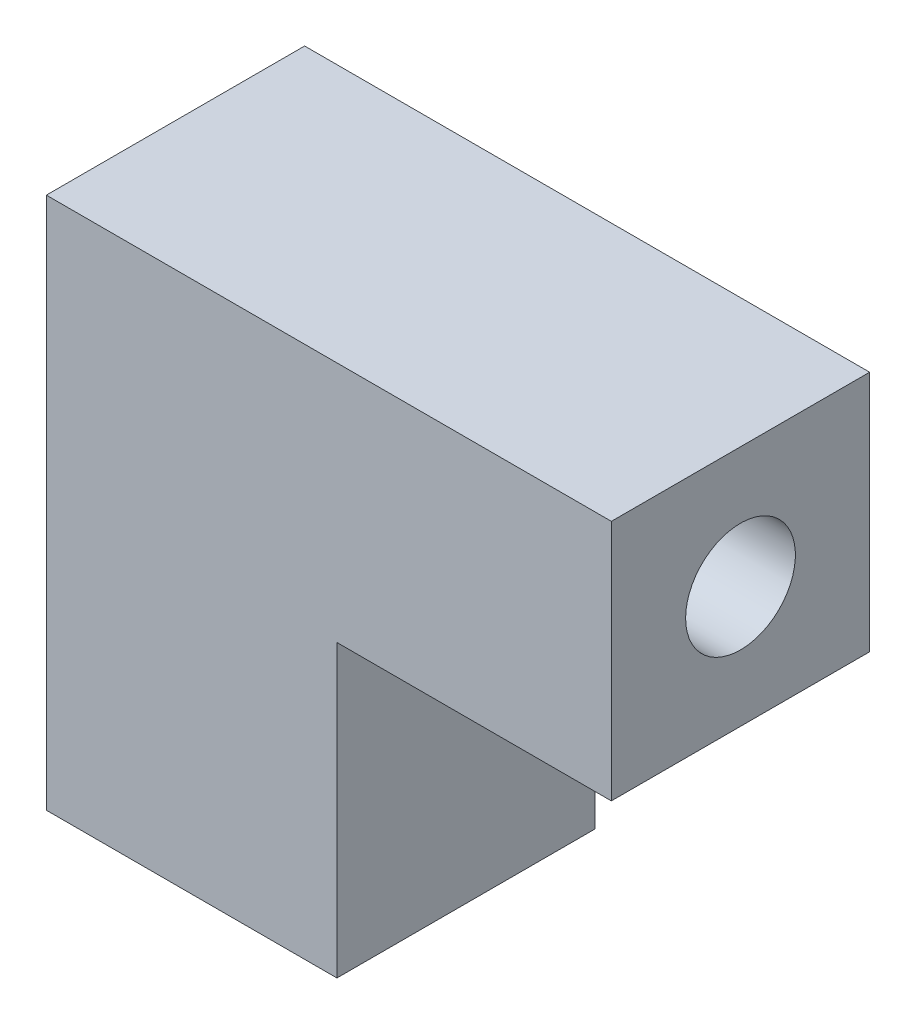
SolidWorks part; units mm, degrees
ref_plane "정면" through (0, 0, 0) normal (0, 0, 1) x (1, 0, 0)
ref_plane "윗면" through (0, 0, 0) normal (0, 1, 0) x (1, 0, 0)
ref_plane "우측면" through (0, 0, 0) normal (1, 0, 0) x (0, 0, -1)
sketch "스케치1" plane through (0, 0, 0) normal (0, 0, 1) x (1, 0, 0)
  line L0 (0, 0) -> (0, 33)
  line L1 (0, 33) -> (35, 33)
  line L2 (35, 33) -> (35, 18)
  line L3 (35, 18) -> (18, 18)
  line L4 (18, 18) -> (18, 0)
  line L5 (18, 0) -> (0, 0)
  dimension "D1" = 35
  dimension "D2" = 15
  dimension "D3" = 33
  dimension "D4" = 17
extrude "보스-돌출1" add sketch "스케치1" along normal mid plane 16
hole_wizard "M8 나사 구멍1" positions "스케치2" profile "스케치3" tap size "M8" standard "KS" end condition through all
sketch "스케치2" plane through (0, 0, 0) normal (-1, 0, 0) x (0, 0, 1)
  line L0 (8, 0) -> (-8, 0) construction
  line L1 (8, 33) -> (8, 0) construction
  point P0 (0, 25.5)
  dimension "D1" = 25.5
  dimension "D2" = 8
sketch "스케치3" plane through (0, 25.5, 0) normal (0, 1, 0) x (0, 0, 1)
  line L0 (0, 0) -> (0, 35)
  line L1 (0, 35) -> (3.4, 35)
  line L2 (3.4, 35) -> (3.4, 0)
  line L5 (3.4, 0) -> (0, 0)
  line L11 (0, -6.35) -> (0, 107.95) construction
  dimension "관통 탭 드릴 지름" = 6.8
  dimension "관통 탭 드릴 깊이" = 35
cosmetic thread "구멍 나사산1" parameters "D2"=8
